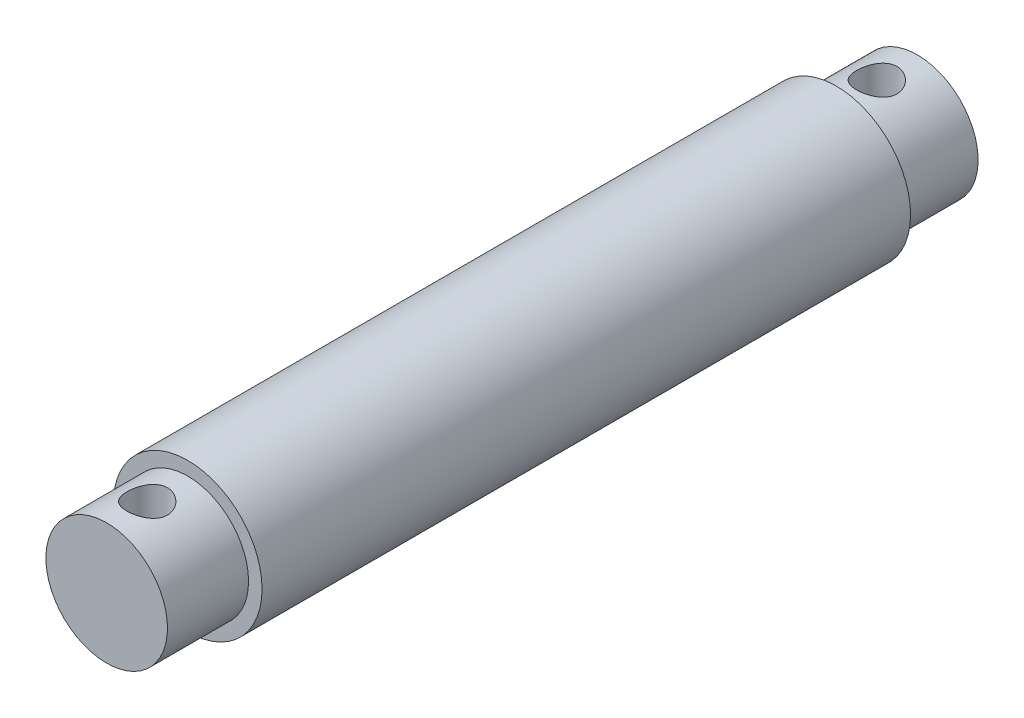
SolidWorks part; units mm, degrees
material "AISI 304"
ref_plane "Front Plane" through (0, 0, 0) normal (0, 0, 1) x (1, 0, 0)
ref_plane "Top Plane" through (0, 0, 0) normal (0, 1, 0) x (1, 0, 0)
ref_plane "Right Plane" through (0, 0, 0) normal (1, 0, 0) x (0, 0, -1)
sketch "Sketch1" plane through (0, 0, 0) normal (0, 0, 1) x (1, 0, 0)
  circle A0 centre (0, 0) radius 5.5
extrude "Boss-Extrude1" add sketch "Sketch1" along normal blind 48
sketch "Sketch2" plane through (0, 0, 48) normal (0, 0, 1) x (1, 0, 0)
  circle A0 centre (0, 0) radius 4.5
  dimension "D1" = 9
extrude "Boss-Extrude2" add sketch "Sketch2" along normal blind 6
sketch "Sketch3" plane through (0, 0, 0) normal (0, 0, -1) x (-1, 0, 0)
  circle A0 centre (0, 0) radius 4.5
extrude "Boss-Extrude3" add sketch "Sketch3" along normal blind 6
sketch "Sketch4" plane through (0, 0, 0) normal (0, 1, 0) x (1, 0, 0)
  line L0 (-4.5, -54) -> (4.5, -54) construction
  line L1 (4.5, 6) -> (-4.5, 6) construction
  circle A0 centre (0, 3) radius 1.5
  circle A1 centre (0, -51) radius 1.5
  dimension "D1" = 3
  dimension "D2" = 3
extrude "Cut-Extrude1" cut sketch "Sketch4" against normal through all both and the other way through all
